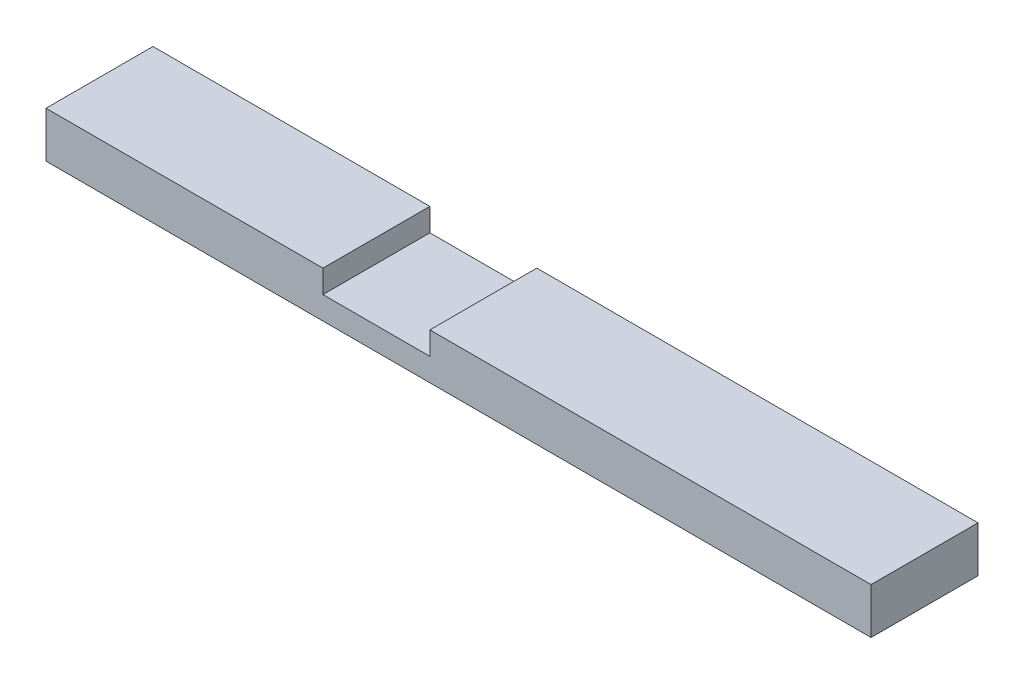
SolidWorks part; units mm, degrees
material "Pine"
ref_plane "Front Plane" through (0, 0, 0) normal (0, 0, 1) x (1, 0, 0)
ref_plane "Top Plane" through (0, 0, 0) normal (0, 1, 0) x (1, 0, 0)
ref_plane "Right Plane" through (0, 0, 0) normal (1, 0, 0) x (0, 0, -1)
sketch "Sketch1" plane through (0, 0, 0) normal (0, 1, 0) x (1, 0, 0)
  line L1 (0, 0) -> (685.8, 0)
  line L2 (0, 0) -> (0, 88.9)
  line L3 (0, 88.9) -> (685.8, 88.9)
  line L4 (685.8, 0) -> (685.8, 88.9)
  dimension "D1" = 88.9
  dimension "D2" = 685.8
extrude "Boss-Extrude1" add sketch "Sketch1" along normal blind 38.1
sketch "Sketch2" plane through (0, 38.1, 0) normal (0, 1, 0) x (1, 0, 0)
  line L0 (685.8, 88.9) -> (0, 88.9) construction
  line L1 (230.1875, 88.9) -> (319.0875, 88.9)
  line L2 (230.1875, 88.9) -> (230.1875, 0)
  line L3 (230.1875, 0) -> (319.0875, 0)
  line L4 (319.0875, 88.9) -> (319.0875, 0)
  line L6 (0, 0) -> (685.8, 0) construction
  dimension "D1" = 88.9
  dimension "D2" = 230.1875
extrude "Cut-Extrude1" cut sketch "Sketch2" against normal blind 19.05
